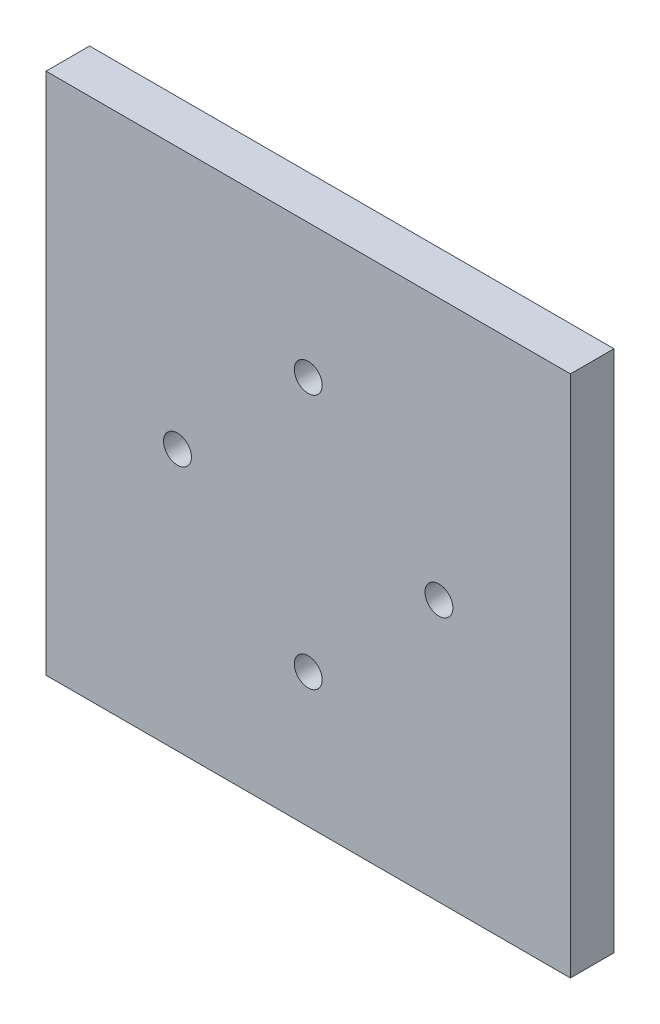
SolidWorks part; units mm, degrees
ref_plane "Front Plane" through (0, 0, 0) normal (0, 0, 1) x (1, 0, 0)
ref_plane "Top Plane" through (0, 0, 0) normal (0, 1, 0) x (1, 0, 0)
ref_plane "Right Plane" through (0, 0, 0) normal (1, 0, 0) x (0, 0, -1)
sketch "Sketch2" plane through (0, 0, 0) normal (0, 0, 1) x (1, 0, 0)
  line L0 (-26.162, 3.175) -> (-18.288, 3.175) construction
  line L1 (-41.3834, -34.9475) -> (35.0334, -34.9475)
  line L2 (-41.3834, -34.9475) -> (-41.3834, 41.2975)
  line L3 (-41.3834, 41.2975) -> (35.0334, 41.2975)
  line L4 (35.0334, -34.9475) -> (35.0334, 41.2975)
  line L5 (-41.3834, -34.9475) -> (35.0334, 41.2975) construction
  line L6 (-41.3834, 41.2975) -> (35.0334, -34.9475) construction
  line L7 (-26.162, 6.35) -> (-26.162, 0) construction
  line L8 (-18.288, 6.35) -> (-18.288, 0) construction
  line L9 (-22.225, 6.35) -> (-22.225, 0) construction
  line L10 (-26.162, 6.35) -> (-18.288, 6.35) construction
  line L11 (-26.162, 0) -> (-18.288, 0) construction
  line L12 (11.938, 3.175) -> (19.812, 3.175) construction
  line L13 (11.938, 6.35) -> (11.938, 0) construction
  line L14 (19.812, 6.35) -> (19.812, 0) construction
  line L15 (-3.175, 25.6947) -> (-3.175, 17.8207) construction
  line L16 (11.938, 6.35) -> (19.812, 6.35) construction
  line L17 (15.875, 6.35) -> (15.875, 0) construction
  line L18 (11.938, 0) -> (19.812, 0) construction
  line L19 (-6.35, 25.6947) -> (0, 25.6947) construction
  line L20 (-6.35, 17.8207) -> (0, 17.8207) construction
  line L21 (-3.175, -11.4707) -> (-3.175, -19.3447) construction
  line L22 (-6.35, 17.8207) -> (-6.35, 25.6947) construction
  line L23 (-6.35, 21.7577) -> (0, 21.7577) construction
  line L24 (0, 17.8207) -> (0, 25.6947) construction
  line L25 (-6.35, -11.4707) -> (0, -11.4707) construction
  line L26 (-6.35, -19.3447) -> (0, -19.3447) construction
  line L27 (-6.35, -15.4077) -> (0, -15.4077) construction
  line L28 (-6.35, -19.3447) -> (-6.35, -11.4707) construction
  line L29 (0, -19.3447) -> (0, -11.4707) construction
  circle A0 centre (-22.225, 3.175) radius 2.032
  circle A1 centre (15.875, 3.175) radius 2.032
  circle A2 centre (-3.175, 21.7577) radius 2.032
  circle A3 centre (-3.175, -15.4077) radius 2.032
  point P0 (-3.175, 3.175)
  dimension "D1" = 4.064
  dimension "D2" = 4.064
  dimension "D3" = 4.064
  dimension "D4" = 4.064
extrude "Boss-Extrude1" add sketch "Sketch2" along normal blind 6.35
